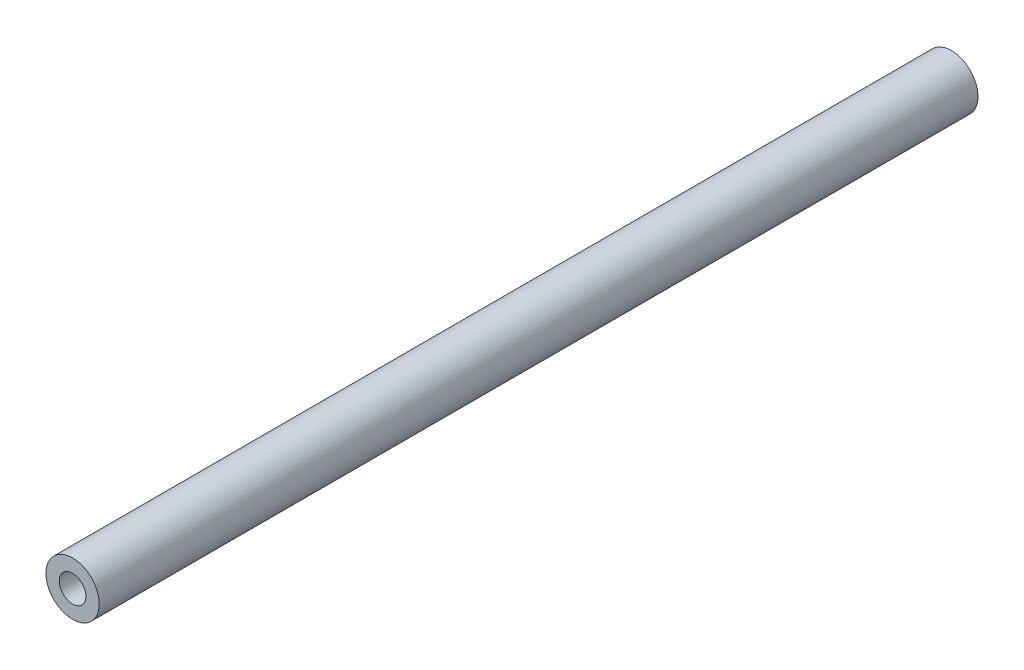
SolidWorks part; units mm, degrees
material "6061-T6 (SS)"
ref_plane "Front Plane" through (0, 0, 0) normal (0, 0, 1) x (1, 0, 0)
ref_plane "Top Plane" through (0, 0, 0) normal (0, 1, 0) x (1, 0, 0)
ref_plane "Right Plane" through (0, 0, 0) normal (1, 0, 0) x (0, 0, -1)
sketch "Sketch1" plane through (0, 0, 0) normal (0, 0, 1) x (1, 0, 0)
  circle A0 centre (0, 0) radius 6.35
  dimension "D1" = 12.7
extrude "Boss-Extrude1" add sketch "Sketch1" along normal mid plane 209.55
sketch "Sketch2" plane through (0, 0, 104.775) normal (0, 0, 1) x (1, 0, 0)
  circle A0 centre (0, 0) radius 3.175
  dimension "D1" = 6.35
sketch "Sketch3" plane through (0, 0, -104.775) normal (0, 0, -1) x (-1, 0, 0)
  circle A0 centre (0, 0) radius 3.175
  dimension "D1" = 6.35
extrude "Cut-Extrude1" cut sketch "Sketch3" against normal blind 19.05
extrude "Cut-Extrude2" cut sketch "Sketch2" against normal blind 19.05
